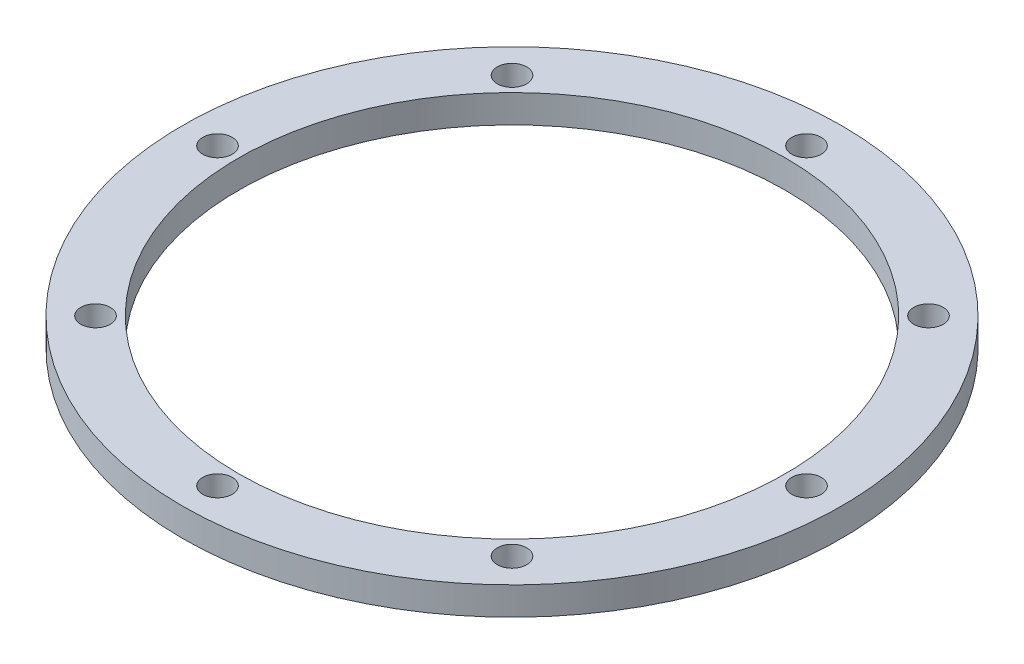
SolidWorks part; units mm, degrees
material "6061-T6 (SS)"
ref_plane "前视基准面" through (0, 0, 0) normal (0, 0, 1) x (1, 0, 0)
ref_plane "上视基准面" through (0, 0, 0) normal (0, 1, 0) x (1, 0, 0)
ref_plane "右视基准面" through (0, 0, 0) normal (1, 0, 0) x (0, 0, -1)
sketch "草图1" plane through (0, 0, 0) normal (0, 0, 1) x (1, 0, 0)
  line L0 (0, 0) -> (0, 24.7963) construction
  line L1 (-39, 0) -> (-47, 0)
  line L2 (-47, 0) -> (-47, 4)
  line L3 (-47, 4) -> (-39, 4)
  line L4 (-39, 4) -> (-39, 0)
  dimension "D1" = 94
  dimension "D2" = 78
  dimension "D3" = 4
revolve "旋转1" add sketch "草图1" angle 360 about L0
sketch "草图2" plane through (0, 0, 0) normal (0, -1, 0) x (1, 0, 0)
  circle A0 centre (0, 0) radius 42 construction
  circle A1 centre (0, 42) radius 2.1
  circle A2 centre (29.6985, 29.6985) radius 2.1
  circle A3 centre (42, 0) radius 2.1
  circle A4 centre (29.6985, -29.6985) radius 2.1
  circle A5 centre (0, -42) radius 2.1
  circle A6 centre (-29.6985, -29.6985) radius 2.1
  circle A7 centre (-42, 0) radius 2.1
  circle A8 centre (-29.6985, 29.6985) radius 2.1
  point P22 (0, 0)
  dimension "D1" = 84
  dimension "D2" = 4.2
  dimension "D3" = 8
extrude "切除-拉伸1" cut sketch "草图2" against normal blind 10
